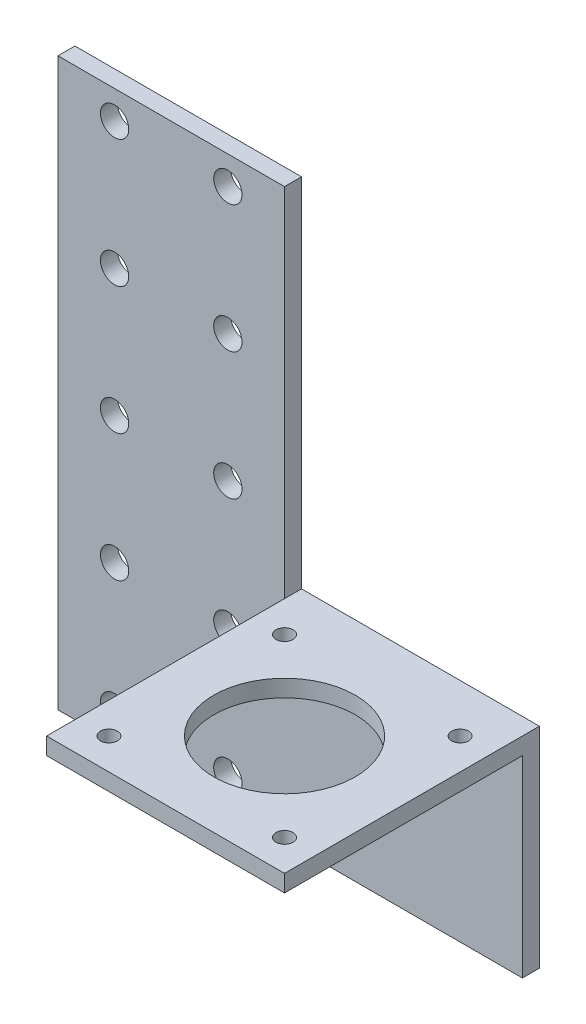
SolidWorks part; units mm, degrees
ref_plane "Front Plane" through (0, 0, 0) normal (0, 0, 1) x (1, 0, 0)
ref_plane "Top Plane" through (0, 0, 0) normal (0, 1, 0) x (1, 0, 0)
ref_plane "Right Plane" through (0, 0, 0) normal (1, 0, 0) x (0, 0, -1)
sketch "Sketch1" plane through (0, 0, 0) normal (0, 0, 1) x (1, 0, 0)
  line L0 (30, -5) -> (10, -5) construction
  line L1 (40, 0) -> (0, 0)
  line L2 (40, 0) -> (40, -66)
  line L3 (82, -100) -> (0, -100)
  line L4 (0, 0) -> (0, -100)
  line L7 (40, -66) -> (82, -66)
  line L8 (82, -100) -> (82, -66)
  line L9 (30, -5) -> (30, -27.5) construction
  line L10 (30, -5) -> (30, 0) construction
  line L11 (30, -95) -> (30, -100) construction
  circle A0 centre (30, -5) radius 2.5
  circle A1 centre (10, -5) radius 2.5
  circle A2 centre (10, -27.5) radius 2.5
  circle A3 centre (10, -50) radius 2.5
  circle A4 centre (10, -72.5) radius 2.5
  circle A5 centre (10, -95) radius 2.5
  circle A6 centre (30, -27.5) radius 2.5
  circle A7 centre (30, -50) radius 2.5
  circle A8 centre (30, -72.5) radius 2.5
  circle A9 centre (30, -95) radius 2.5
  point P21 (35.0848, -100)
  point P32 (32.4012, -37.6266)
  dimension "D9" = 5
  dimension "D10" = 10
  dimension "D1" = 40
  dimension "D2" = 42
  dimension "D3" = 100
  dimension "D4" = 34
  dimension "D7" = 20
  dimension "D8" = 5
  dimension "D5" = 2
  dimension "D6" = 5
extrude "Boss-Extrude1" add sketch "Sketch1" along normal blind 3
sketch "Sketch2" plane through (0, -66, 0) normal (0, 1, 0) x (1, 0, 0)
  line L0 (40, -3) -> (40, 0) construction
  line L1 (82, 0) -> (40, 0)
  line L2 (82, 0) -> (82, -45)
  line L3 (82, -45) -> (40, -45)
  line L4 (40, 0) -> (40, -45)
  line L5 (82, -3) -> (40, -3) construction
  dimension "D1" = 42
extrude "Boss-Extrude2" add sketch "Sketch2" along normal blind 3
sketch "Sketch3" plane through (0, -66, 0) normal (0, -1, 0) x (1, 0, 0)
  line L0 (40, 3) -> (40, 45) construction
  line L1 (40, 45) -> (82, 45) construction
  line L2 (61, 24) -> (40, 45) construction
  circle A0 centre (61, 24) radius 12.5
  circle A2 centre (45.5, 39.5) radius 1.5
  circle A3 centre (45.5, 8.5) radius 1.5
  circle A4 centre (76.5, 8.5) radius 1.5
  circle A5 centre (76.5, 39.5) radius 1.5
  point P5 (40, 24)
  point P8 (44.2487, 8.5781)
  point P9 (61, 45)
  point P13 (61, 24)
  point P21 (61, 24)
  dimension "D2" = 15.5
  dimension "D3" = 3
  dimension "D4" = 25
  dimension "D1" = 4
extrude "Cut-Extrude1" cut sketch "Sketch3" against normal blind 13
